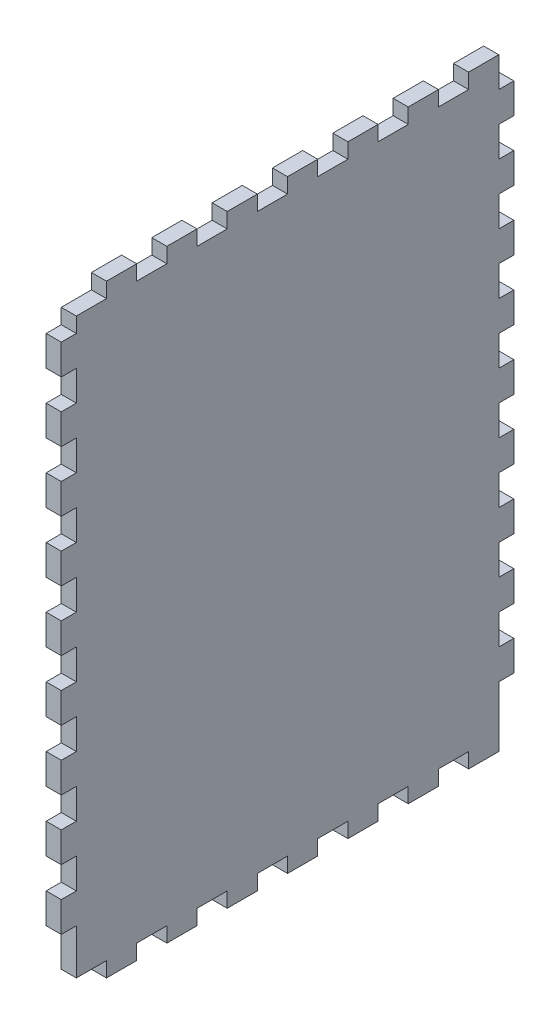
SolidWorks part; units mm, degrees
ref_plane "Front Plane" through (0, 0, 0) normal (0, 0, 1) x (1, 0, 0)
ref_plane "Top Plane" through (0, 0, 0) normal (0, 1, 0) x (1, 0, 0)
ref_plane "Right Plane" through (0, 0, 0) normal (1, 0, 0) x (0, 0, -1)
sketch "Sketch1" plane through (0, 0, 0) normal (1, 0, 0) x (0, 0, -1)
  line L1 (95.25, 127) -> (-95.25, 127)
  line L2 (95.25, 127) -> (95.25, -127)
  line L3 (95.25, -127) -> (-95.25, -127)
  line L4 (-95.25, 127) -> (-95.25, -127)
  line L5 (95.25, 127) -> (-95.25, -127) construction
  line L6 (95.25, -127) -> (-95.25, 127) construction
  point P0 (0, 0)
  dimension "D1" = 254
  dimension "D2" = 190.5
extrude "Boss-Extrude1" add sketch "Sketch1" along normal blind 6.35
sketch "Sketch2" plane through (0, 0, 0) normal (-1, 0, 0) x (0, 0, 1)
  line L0 (-95.25, -127) -> (-95.25, 127) construction
  line L1 (-95.25, -88.9) -> (-88.9, -88.9)
  line L2 (-95.25, -88.9) -> (-95.25, -76.2)
  line L3 (-95.25, -76.2) -> (-88.9, -76.2)
  line L4 (-88.9, -88.9) -> (-88.9, -76.2)
  dimension "D1" = 6.35
  dimension "D2" = 12.7
  dimension "D3" = 38.1
extrude "Cut-Extrude1" cut sketch "Sketch2" against normal through all
pattern_linear "LPattern1" count 9 spacing 25.4 along (0, 1, 0) of "Cut-Extrude1"
mirror "Mirror1" about plane through (0, 0, 0) normal (0, 0, 1) of "LPattern1", "Cut-Extrude1"
sketch "Sketch3" plane through (0, 0, 0) normal (-1, 0, 0) x (0, 0, 1)
  line L0 (95.25, -127) -> (-95.25, -127) construction
  line L1 (-76.2, -127) -> (-63.5, -127)
  line L2 (-76.2, -127) -> (-76.2, -120.65)
  line L3 (-76.2, -120.65) -> (-63.5, -120.65)
  line L4 (-63.5, -127) -> (-63.5, -120.65)
  dimension "D1" = 12.7
  dimension "D2" = 6.35
  dimension "D3" = 19.05
extrude "Cut-Extrude2" cut sketch "Sketch3" against normal through all
pattern_linear "LPattern2" count 7 spacing 25.4 along (0, 0, 1) of "Cut-Extrude2"
mirror "Mirror2" about plane through (0, 0, 0) normal (0, 1, 0) of "LPattern2", "Cut-Extrude2"
sketch "Sketch4" plane through (0, 0, 0) normal (-1, 0, 0) x (0, 0, 1)
  line L1 (-95.25, -127) -> (-88.9, -127)
  line L2 (-95.25, -127) -> (-95.25, -101.6)
  line L3 (-95.25, -101.6) -> (-88.9, -101.6)
  line L4 (-88.9, -127) -> (-88.9, -101.6)
  dimension "D1" = 25.4
  dimension "D2" = 6.35
extrude "Cut-Extrude3" cut sketch "Sketch4" against normal through all
mirror "Mirror3" about plane through (0, 0, 0) normal (0, 0, 1) of "Cut-Extrude3"
